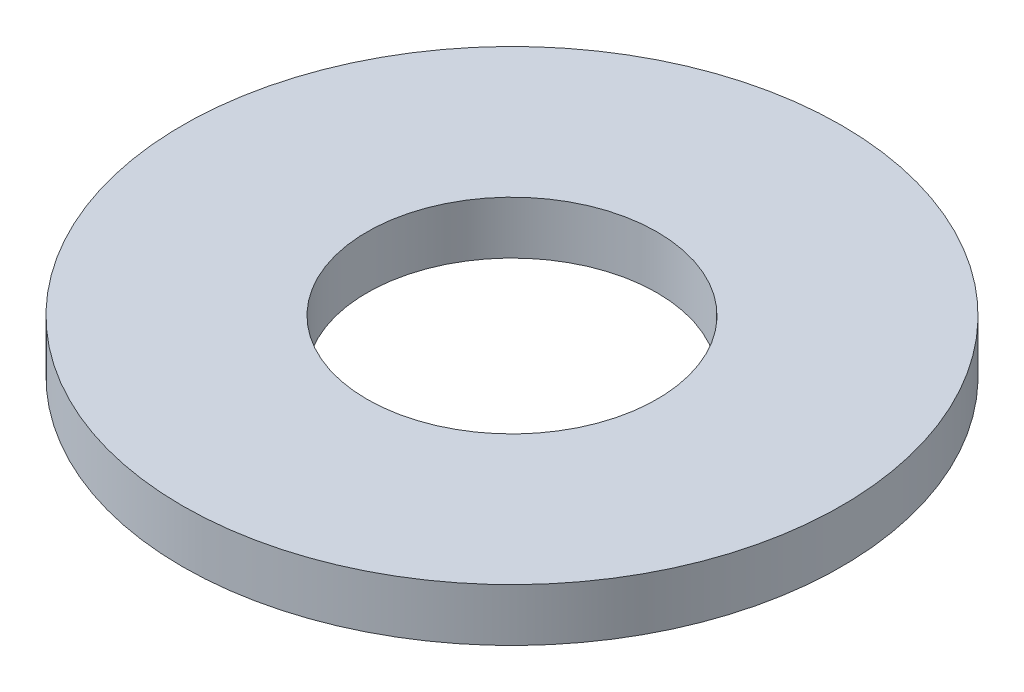
SolidWorks part; units mm, degrees
ref_plane "Front Plane" through (0, 0, 0) normal (0, 0, 1) x (1, 0, 0)
ref_plane "Top Plane" through (0, 0, 0) normal (0, 1, 0) x (1, 0, 0)
ref_plane "Right Plane" through (0, 0, 0) normal (1, 0, 0) x (0, 0, -1)
sketch "Sketch1" plane through (0, 0, 0) normal (0, 1, 0) x (1, 0, 0)
  circle A0 centre (0, 0) radius 2.5
  dimension "OD" = 5
extrude "Boss-Extrude1" add sketch "Sketch1" along normal blind 0.4
sketch "Sketch5" plane through (0, 0.4, 0) normal (0, 1, 0) x (-1, 0, 0)
  circle A0 centre (0, 0) radius 1.1
  dimension "ID" = 2.2
extrude "Cut-Extrude1" cut sketch "Sketch5" against normal through all
